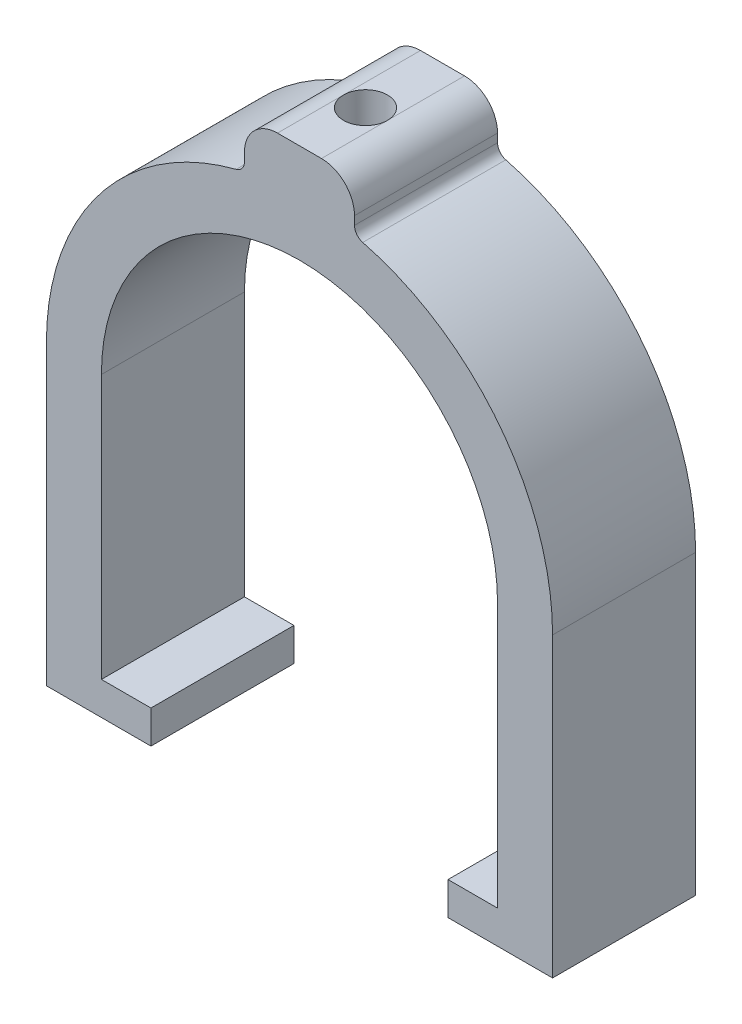
SolidWorks part; units mm, degrees
ref_plane "Front Plane" through (0, 0, 0) normal (0, 0, 1) x (1, 0, 0)
ref_plane "Top Plane" through (0, 0, 0) normal (0, 1, 0) x (1, 0, 0)
ref_plane "Right Plane" through (0, 0, 0) normal (1, 0, 0) x (0, 0, -1)
sketch "Sketch1" plane through (0, 0, 0) normal (0, 0, 1) x (1, 0, 0)
  line L0 (0, 0) -> (0, 75.8919) construction
  line L1 (-13.5, 0) -> (-23, 0)
  line L2 (-23, 0) -> (-23, 27)
  line L3 (-13.5, 0) -> (-13.5, 3)
  line L4 (-13.5, 3) -> (-18, 3)
  line L5 (-18, 3) -> (-18, 27)
  line L6 (13.5, 0) -> (23, 0)
  line L7 (13.5, 0) -> (13.5, 3)
  line L8 (13.5, 3) -> (18, 3)
  line L9 (18, 3) -> (18, 27)
  line L10 (23, 0) -> (23, 27)
  line L11 (-5, 50.2379) -> (-5, 51)
  line L12 (-2, 54) -> (2, 54)
  line L13 (5, 51) -> (5, 50.2379)
  arc A0 (-5.75, 49.2697) -> (-23, 27) centre (0, 27) ccw
  arc A1 (0, 45) -> (-18, 27) centre (0, 27) ccw
  arc A2 (5.75, 49.2697) -> (23, 27) centre (0, 27) cw
  arc A3 (0, 45) -> (18, 27) centre (0, 27) cw
  arc A4 (2, 54) -> (5, 51) centre (2, 51) cw
  arc A5 (-5, 51) -> (-2, 54) centre (-2, 51) cw
  arc A6 (0, 50) -> (-23, 27) centre (0, 27) ccw construction
  arc A7 (5, 50.2379) -> (5.75, 49.2697) centre (6, 50.2379) ccw
  arc A8 (-5, 50.2379) -> (-5.75, 49.2697) centre (-6, 50.2379) cw
  point P11 (-5, 49.4499)
  point P14 (0, 50)
  point P25 (5, 49.4499)
  point P28 (5, 54)
  point P31 (-5, 54)
  point P36 (0, 0)
  point P37 (0, 0)
  point P38 (0, 0)
  point P39 (-1.4671, 44.9401)
  point P40 (0, 0)
  point P41 (0, 0)
  point P42 (0, 0)
  point P43 (0, 45)
  dimension "D5" = 46
  dimension "D9" = 3
  dimension "D10" = 1
  dimension "D1" = 23
  dimension "D2" = 13.5
  dimension "D3" = 3
  dimension "D4" = 5
  dimension "D6" = 50
  dimension "D7" = 10
  dimension "D8" = 4
extrude "Boss-Extrude2" add sketch "Sketch1" along normal mid plane 13
sketch "Sketch3" plane through (0, 0, 0) normal (0, 1, 0) x (1, 0, 0)
  line L0 (-23, -6.5) -> (-5.75, -6.5) construction
  line L1 (-23, -6.5) -> (-23, 6.5) construction
  circle A0 centre (0, -0.5) radius 2
  dimension "D1" = 4
  dimension "D2" = 6
  dimension "D3" = 23
extrude "Cut-Extrude1" cut sketch "Sketch3" against normal up to next from surface
